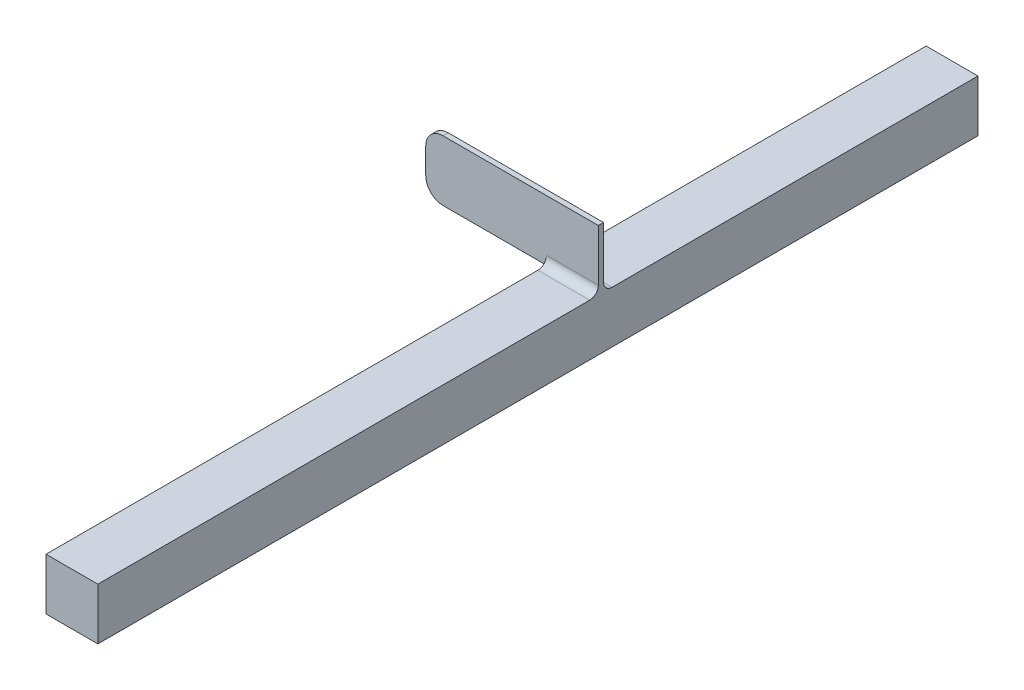
SolidWorks part; units mm, degrees
ref_plane "Plano frontal" through (0, 0, 0) normal (0, 0, 1) x (1, 0, 0)
ref_plane "Plano superior" through (0, 0, 0) normal (0, 1, 0) x (1, 0, 0)
ref_plane "Plano direito" through (0, 0, 0) normal (1, 0, 0) x (0, 0, -1)
sketch "Esboço2" plane through (0, 0, 0) normal (0, 0, 1) x (1, 0, 0)
  line L1 (-110.6583, 30) -> (-80.6129, 30)
  line L2 (-110.6583, 30) -> (-110.6583, 0)
  line L3 (-110.6583, 0) -> (-80.6129, 0)
  line L4 (-80.6129, 30) -> (-80.6129, 0)
  dimension "D1" = 30
  dimension "D2" = 30.0454
extrude "Ressalto-extrusão1" add sketch "Esboço2" along normal mid plane 510
ref_plane "Plano1" through (0, 0, -35) normal (0, 0, 1) x (1, 0, 0)
sketch "Esboço3" plane through (0, 0, -35) normal (0, 0, 1) x (1, 0, 0)
  line L1 (-80.6129, 30) -> (-180.6129, 30)
  line L2 (-80.6129, 30) -> (-80.6129, 65)
  line L3 (-80.6129, 65) -> (-180.6129, 65)
  line L4 (-180.6129, 30) -> (-180.6129, 65)
  point P5 (0, 0)
  dimension "D1" = 35
  dimension "D2" = 100
extrude "Ressalto-extrusão2" add sketch "Esboço3" along normal blind 0.001 and the other way blind 3
fillet "Filete1" radius 5 2 edges at (-95.6356, 30, -38) (-95.6356, 30, -34.999)
fillet "Filete2" radius 10 2 edges at (-180.6129, 30, -36.4995) (-180.6129, 65, -36.4995)
